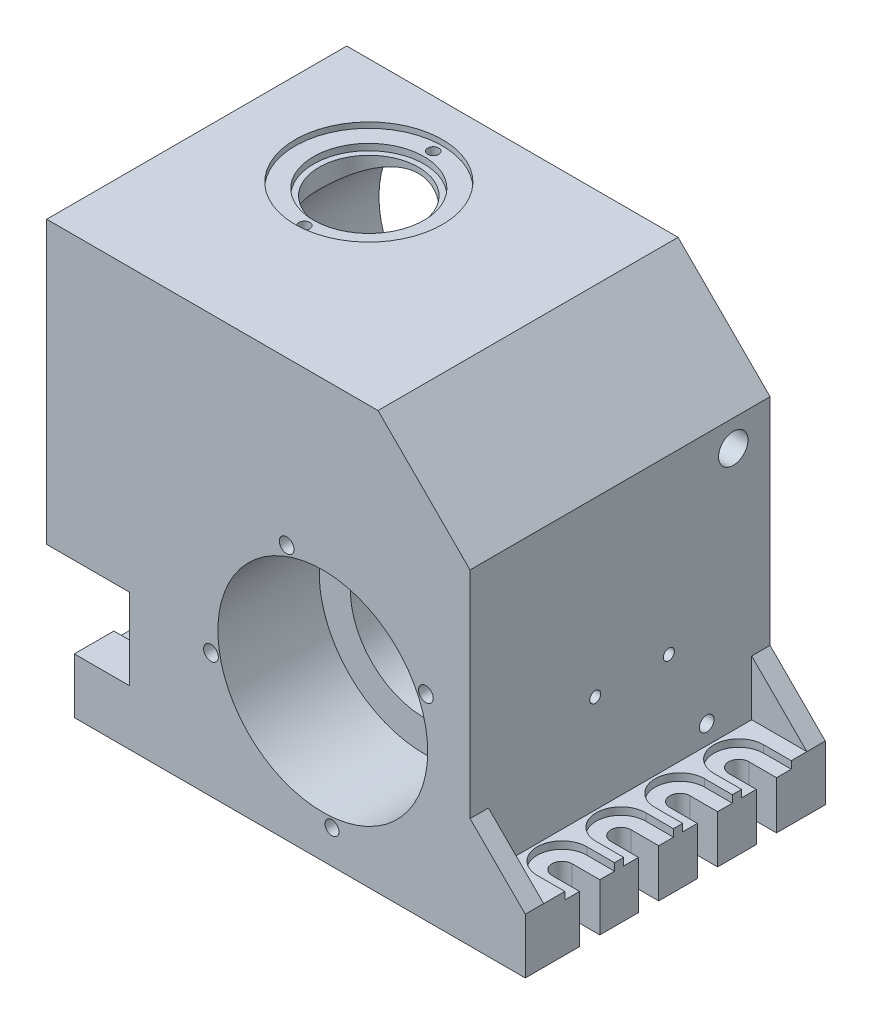
SolidWorks part; units mm, degrees
ref_plane "前视基准面" through (0, 0, 0) normal (0, 0, 1) x (1, 0, 0)
ref_plane "上视基准面" through (0, 0, 0) normal (0, 1, 0) x (1, 0, 0)
ref_plane "右视基准面" through (0, 0, 0) normal (1, 0, 0) x (0, 0, -1)
sketch "草图1" plane through (0, 0, 0) normal (0, 0, 1) x (1, 0, 0)
  line L0 (110, -80) -> (-105, -80)
  line L1 (-105, -80) -> (-105, -6)
  line L2 (-105, -6) -> (-150, -6)
  line L3 (-150, -6) -> (-150, 147)
  line L4 (-150, 147) -> (30, 147)
  line L5 (30, 147) -> (80, 97)
  line L6 (80, 97) -> (80, -20)
  line L7 (80, -20) -> (110, -50)
  line L8 (110, -50) -> (110, -80)
  circle A0 centre (0, 0) radius 60 construction
  dimension "D1" = 120
  dimension "D2" = 180
  dimension "D3" = 150
  dimension "D4" = 153
  dimension "D5" = 227
  dimension "D6" = 80
  dimension "D7" = 80
  dimension "D8" = 215
  dimension "D9" = 45
  dimension "D10" = 30
  dimension "D11" = 60
  dimension "D12" = 30
extrude "凸台-拉伸1" add sketch "草图1" along normal blind 163
sketch "草图2" plane through (110, 0, 0) normal (1, 0, 0) x (0, 0, -1)
  line L0 (-81.5, -80) -> (-81.5, 123.6625) construction
  line L1 (-163, -80) -> (0, -80) construction
  line L2 (-163, -20) -> (0, -20) construction
  line L3 (-153, -20) -> (-10, -20)
  line L4 (-153, -20) -> (-153, -50)
  line L5 (-153, -50) -> (-10, -50)
  line L6 (-10, -20) -> (-10, -50)
  line L7 (-163, -50) -> (0, -50) construction
  line L8 (0, -50) -> (0, -20) construction
  line L9 (-163, -50) -> (-163, -20) construction
  point P12 (0, -35)
  point P15 (-163, -35)
  dimension "D1" = 10
  dimension "D2" = 10
extrude "切除-拉伸1" cut sketch "草图2" against normal up to surface (30 mm away) up to face at (80, 38.5, 81.5)
sketch "草图3" plane through (110, 0, 0) normal (1, 0, 0) x (0, 0, -1)
  line L1 (-64, -80) -> (-64, -50) construction
  line L2 (-32, -80) -> (-32, -50)
  line L3 (-32, -80) -> (-32, -50) construction
  line L4 (-96, -80) -> (-96, -50) construction
  line L5 (-128, -80) -> (-128, -50) construction
  line L6 (-26.5, -80) -> (-26.5, -50)
  line L7 (-58.5, -80) -> (-58.5, -50)
  line L8 (-90.5, -80) -> (-90.5, -50)
  line L9 (-122.5, -80) -> (-122.5, -50)
  line L10 (-37.5, -80) -> (-37.5, -50)
  line L11 (-69.5, -80) -> (-69.5, -50)
  line L12 (-101.5, -80) -> (-101.5, -50)
  line L13 (-133.5, -80) -> (-133.5, -50)
  line L14 (-153, -50) -> (-10, -50) construction
  line L15 (-133.5, -50) -> (-122.5, -50)
  line L16 (-163, -80) -> (0, -80) construction
  line L17 (-133.5, -80) -> (-122.5, -80)
  line L18 (-101.5, -50) -> (-90.5, -50)
  line L19 (-101.5, -80) -> (-90.5, -80)
  line L20 (-69.5, -50) -> (-58.5, -50)
  line L21 (-69.5, -80) -> (-58.5, -80)
  line L22 (-37.5, -50) -> (-26.5, -50)
  line L23 (-37.5, -80) -> (-26.5, -80)
  dimension "D1" = 32
  dimension "D2" = 32
  dimension "D3" = 32
  dimension "D4" = 32
  dimension "D5" = 5.5
  dimension "D6" = 5.5
extrude "切除-拉伸2" cut sketch "草图3" against normal blind 15
sketch "草图4" plane through (0, -50, 0) normal (0, 1, 0) x (1, 0, 0)
  line L0 (95, -26.5) -> (95, -37.5) construction
  line L1 (95, -58.5) -> (95, -69.5) construction
  line L2 (95, -90.5) -> (95, -101.5) construction
  line L3 (95, -122.5) -> (95, -133.5) construction
  circle A0 centre (95, -32) radius 5.5
  circle A1 centre (95, -64) radius 5.5
  circle A2 centre (95, -96) radius 5.5
  circle A3 centre (95, -128) radius 5.5
extrude "切除-拉伸3" cut sketch "草图4" against normal blind 40
sketch "草图5" plane through (0, -50, 0) normal (0, 1, 0) x (1, 0, 0)
  line L43 (95, -77.5) -> (110, -77.5)
  line L44 (110, -50.5) -> (95, -50.5)
  line L45 (95, -45.5) -> (110, -45.5)
  line L46 (110, -18.5) -> (95, -18.5)
  line L47 (95, -45.5) -> (110, -45.5)
  line L48 (110, -18.5) -> (95, -18.5)
  line L49 (95, -109.5) -> (110, -109.5)
  line L50 (110, -82.5) -> (95, -82.5)
  line L51 (95, -141.5) -> (110, -141.5)
  line L52 (110, -114.5) -> (95, -114.5)
  line L53 (110, -18.5) -> (110, -45.5)
  line L54 (110, -114.5) -> (110, -141.5)
  line L55 (110, -82.5) -> (110, -109.5)
  line L56 (110, -50.5) -> (110, -77.5)
  arc A24 (95, -50.5) -> (95, -77.5) centre (95, -64) ccw
  arc A25 (95, -18.5) -> (95, -45.5) centre (95, -32) ccw
  arc A26 (95, -18.5) -> (95, -45.5) centre (95, -32) ccw
  arc A27 (95, -82.5) -> (95, -109.5) centre (95, -96) ccw
  arc A28 (95, -114.5) -> (95, -141.5) centre (95, -128) ccw
  dimension "D1" = 8
  dimension "D2" = 4
extrude "切除-拉伸4" cut sketch "草图5" against normal blind 4
sketch "草图6" plane through (0, 0, 163) normal (0, 0, 1) x (1, 0, 0)
  circle A0 centre (0, 0) radius 40
  dimension "D1" = 80
extrude "切除-拉伸5" cut sketch "草图6" against normal blind 248
sketch "草图7" plane through (0, 0, 163) normal (0, 0, 1) x (1, 0, 0)
  circle A0 centre (0, 0) radius 57
  dimension "D1" = 114
extrude "切除-拉伸6" cut sketch "草图7" against normal blind 55
sketch "草图8" plane through (0, 0, 163) normal (0, 0, 1) x (1, 0, 0)
  circle A0 centre (-19.6334, 58.8093) radius 4
  circle A1 centre (56.0139, 26.5789) radius 4
  circle A2 centre (-60.747, -12.4016) radius 4
  circle A3 centre (4.9889, -61.799) radius 3.7856
  circle A4 centre (4.9889, -61.799) radius 3.7856 construction
  circle A5 centre (-60.747, -12.4016) radius 4 construction
  circle A6 centre (56.0139, 26.5789) radius 4 construction
  circle A7 centre (-19.6334, 58.8093) radius 4 construction
extrude "切除-拉伸7" cut sketch "草图8" against normal blind 18
sketch "草图10" plane through (0, 0, 0) normal (0, 0, -1) x (-1, 0, 0)
  circle A0 centre (0, 0) radius 64.5
  dimension "D1" = 129
extrude "切除-拉伸8" cut sketch "草图10" against normal blind 54
sketch "草图11" plane through (0, 0, 0) normal (0, 0, -1) x (-1, 0, 0)
  circle A0 centre (0, 85) radius 42.5
  dimension "D1" = 85
  dimension "D2" = 85
extrude "切除-拉伸9" cut sketch "草图11" against normal blind 103
sketch "草图12" plane through (0, 0, 103) normal (0, 0, -1) x (-1, 0, 0)
  circle A0 centre (0, 85) radius 10
  dimension "D1" = 20
extrude "切除-拉伸10" cut sketch "草图12" against normal blind 44
sketch "草图13" plane through (0, 0, 103) normal (0, 0, -1) x (-1, 0, 0)
  circle A0 centre (0, 85) radius 21.5
  dimension "D1" = 43
extrude "切除-拉伸11" cut sketch "草图13" against normal blind 30
sketch "草图14" plane through (0, 0, 133) normal (0, 0, -1) x (-1, 0, 0)
  circle A0 centre (0, 85) radius 17.5
  dimension "D1" = 35
extrude "切除-拉伸12" cut sketch "草图14" against normal blind 11
sketch "草图15" plane through (0, 0, 163) normal (0, 0, 1) x (1, 0, 0)
  line L1 (-105, -80) -> (-135, -80)
  line L2 (-105, -80) -> (-105, -50)
  line L3 (-105, -50) -> (-135, -50)
  line L4 (-135, -80) -> (-135, -50)
  dimension "D1" = 30
  dimension "D2" = 30
extrude "凸台-拉伸2" add sketch "草图15" against normal up to surface (163 mm away) up to face at (0, 31.5, 0)
ref_plane "基准面1" through (-12.5, 0, 0) normal (1, 0, 0) x (0, 0, -1)
mirror "镜向1" about plane through (-12.5, 0, 0) normal (1, 0, 0) of "切除-拉伸2", "切除-拉伸3", "切除-拉伸4"
sketch "草图16" plane through (0, 0, 0) normal (0, 0, -1) x (-1, 0, 0)
  circle A0 centre (80, 85) radius 44.5
  circle A1 centre (0, 85) radius 42.5 construction
  dimension "D1" = 80
  dimension "D2" = 89
extrude "切除-拉伸13" cut sketch "草图16" against normal blind 16
sketch "草图17" plane through (0, 0, 16) normal (0, 0, -1) x (-1, 0, 0)
  circle A0 centre (80, 85) radius 52.5
  dimension "D1" = 105
extrude "切除-拉伸14" cut sketch "草图17" against normal blind 82 and the other way blind 16
sketch "草图18" plane through (0, 0, 98) normal (0, 0, -1) x (-1, 0, 0)
  circle A0 centre (80, 85) radius 21.5
  dimension "D1" = 43
extrude "切除-拉伸15" cut sketch "草图18" against normal blind 29
sketch "草图19" plane through (0, 0, 127) normal (0, 0, -1) x (-1, 0, 0)
  circle A0 centre (80, 85) radius 17.5
  dimension "D1" = 35
extrude "切除-拉伸16" cut sketch "草图19" against normal blind 11
sketch "草图20" plane through (0, 0, 138) normal (0, 0, -1) x (-1, 0, 0)
  circle A0 centre (80, 85) radius 10
  dimension "D1" = 20
extrude "切除-拉伸17" cut sketch "草图20" against normal blind 3
sketch "草图21" plane through (0, 0, 0) normal (0, 0, -1) x (-1, 0, 0)
  circle A0 centre (140, 137) radius 4
  circle A1 centre (95, -65) radius 4
  circle A2 centre (-70, -65) radius 4
  circle A3 centre (-70, 87) radius 4
  circle A4 centre (140, 137) radius 4 construction
  circle A5 centre (95, -65) radius 4 construction
  circle A6 centre (-70, -65) radius 4 construction
  circle A7 centre (-70, 87) radius 4 construction
extrude "切除-拉伸18" cut sketch "草图21" against normal blind 9
sketch "草图22" plane through (0, 0, 0) normal (0, 0, -1) x (-1, 0, 0)
  line L0 (-30, 147) -> (150, 147) construction
  line L1 (150, 147) -> (150, -6) construction
  line L2 (150, -6) -> (105, -6) construction
  circle A0 centre (140, 4) radius 4.14
  circle A1 centre (32, 137) radius 4.14
  dimension "D1" = 62
  dimension "D2" = 8.28
  dimension "D3" = 10
  dimension "D4" = 10
  dimension "D5" = 10
  dimension "D6" = 8.28
extrude "切除-拉伸19" cut sketch "草图22" against normal blind 10
sketch "草图23" plane through (0, 0, 54) normal (0, 0, -1) x (-1, 0, 0)
  line L0 (29.3558, 34.151) -> (59.4932, 64.2885)
  line L1 (59.4932, 64.2885) -> (34.6633, 89.1184)
  line L2 (34.6633, 89.1184) -> (14.4588, 44.9952)
  line L3 (14.4588, 44.9952) -> (29.3558, 34.151)
extrude "切除-拉伸20" cut sketch "草图23" along normal blind 120
fillet "圆角1" radius 15 4 edges at (-34.0625, 59.5835, 76) (31.3888, 56.3471, 27) (-34.0625, 110.4165, 49) (-47.0192, 44.1525, 27)
sketch "草图24" plane through (0, 147, 0) normal (0, 1, 0) x (1, 0, 0)
  line L0 (-150, -163) -> (-150, 0) construction
  line L2 (30, 0) -> (-150, 0) construction
  circle A0 centre (-80, -58) radius 27
  dimension "D1" = 54
  dimension "D2" = 70
  dimension "D3" = 58
extrude "切除-拉伸21" cut sketch "草图24" against normal blind 30
sketch "草图25" plane through (0, 147, 0) normal (0, 1, 0) x (1, 0, 0)
  circle A0 centre (-80, -58) radius 30
  dimension "D1" = 60
extrude "切除-拉伸22" cut sketch "草图25" against normal blind 6.5
sketch "草图26" plane through (0, 147, 0) normal (0, 1, 0) x (1, 0, 0)
  circle A0 centre (-80, -58) radius 40
  dimension "D1" = 80
extrude "切除-拉伸23" cut sketch "草图26" against normal blind 3
sketch "草图27" plane through (0, 144, 0) normal (0, 1, 0) x (1, 0, 0)
  line L0 (-80, -58) -> (-60.5589, -58) construction
  circle A0 centre (-80, -23) radius 3
  circle A1 centre (-80, -93) radius 3
  dimension "D1" = 6
  dimension "D2" = 70
extrude "切除-拉伸24" cut sketch "草图27" against normal blind 8
sketch "草图28" plane through (80, 0, 0) normal (1, 0, 0) x (0, 0, -1)
  circle A0 centre (-95, 3.23) radius 3
  circle A1 centre (-55, 3.23) radius 3
  circle A2 centre (-55, 3.23) radius 6 construction
  circle A3 centre (-95, 3.23) radius 6 construction
  dimension "D1" = 6
  dimension "D2" = 6
extrude "切除-拉伸25" cut sketch "草图28" against normal blind 8
sketch "草图29" plane through (80, 0, 0) normal (1, 0, 0) x (0, 0, -1)
  circle A0 centre (-34.4343, -39.5704) radius 4
  dimension "D1" = 8
extrude "切除-拉伸26" cut sketch "草图29" against normal blind 37
sketch "草图30" plane through (80, 0, 0) normal (1, 0, 0) x (0, 0, -1)
  line L0 (0, -20) -> (0, 97) construction
  circle A0 centre (-20, 82.7053) radius 8
  dimension "D1" = 16
  dimension "D2" = 20
extrude "切除-拉伸27" cut sketch "草图30" against normal blind 48
